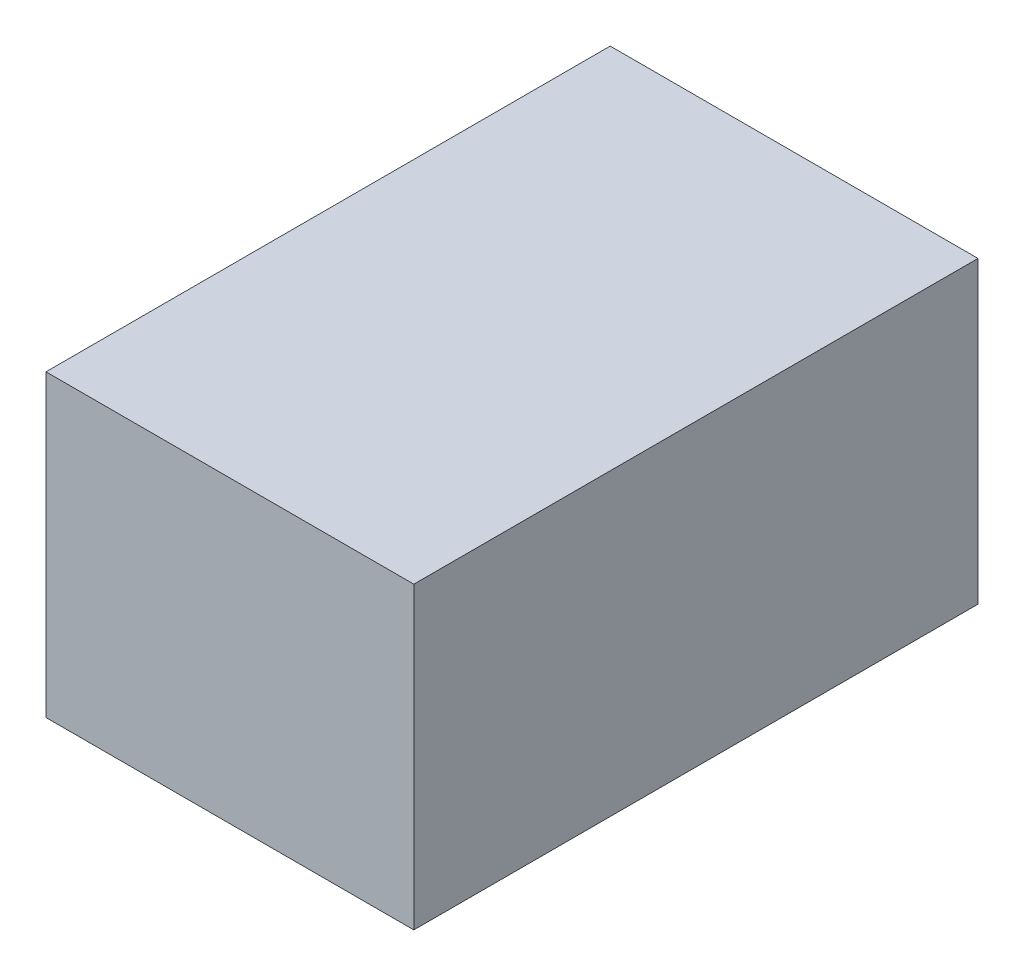
SolidWorks part; units mm, degrees
ref_plane "Front Plane" through (0, 0, 0) normal (0, 0, 1) x (1, 0, 0)
ref_plane "Top Plane" through (0, 0, 0) normal (0, 1, 0) x (1, 0, 0)
ref_plane "Right Plane" through (0, 0, 0) normal (1, 0, 0) x (0, 0, -1)
sketch "Sketch1" plane through (0, 0, 0) normal (0, 0, 1) x (1, 0, 0)
  line L1 (-109.2, 88.9) -> (109.2, 88.9)
  line L2 (-109.2, 88.9) -> (-109.2, -88.9)
  line L3 (-109.2, -88.9) -> (109.2, -88.9)
  line L4 (109.2, 88.9) -> (109.2, -88.9)
  line L5 (-109.2, 88.9) -> (109.2, -88.9) construction
  line L6 (-109.2, -88.9) -> (109.2, 88.9) construction
  point P0 (0, 0)
  dimension "D1" = 218.4
  dimension "D2" = 177.8
extrude "Boss-Extrude1" add sketch "Sketch1" along normal blind 335
